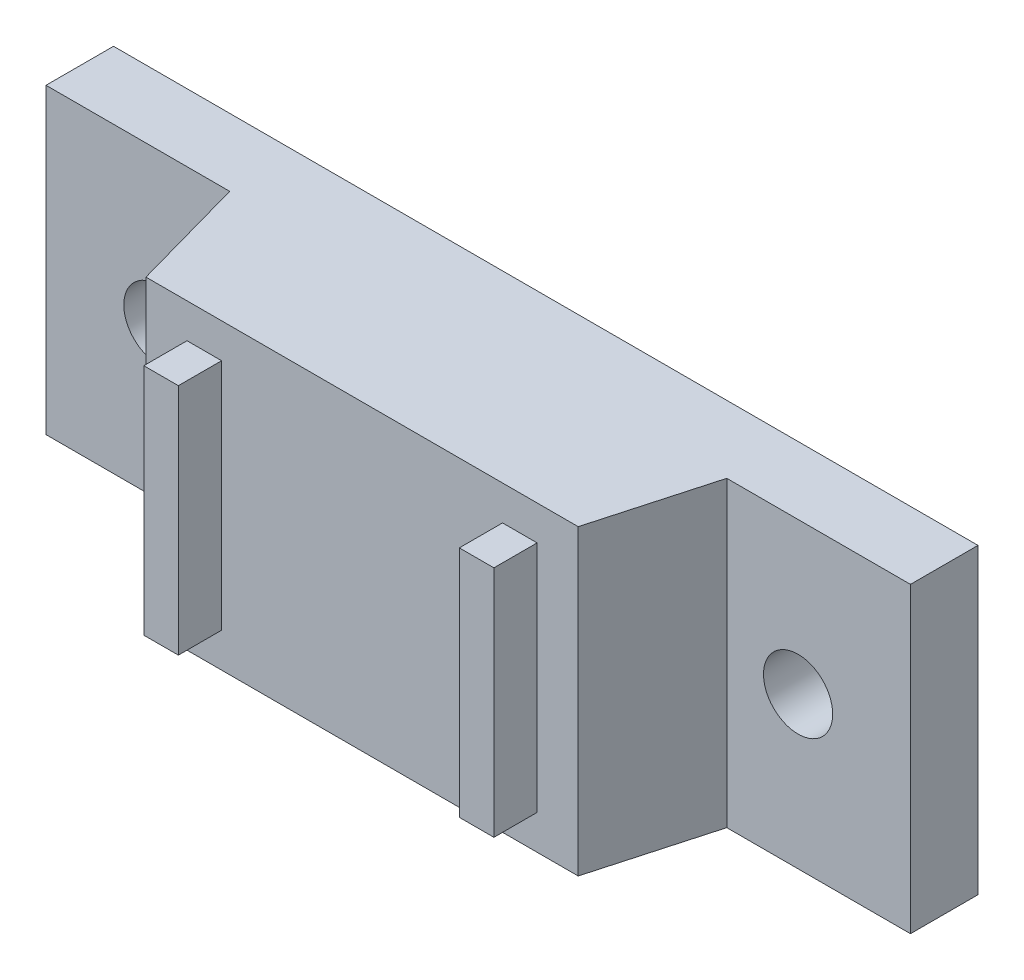
SolidWorks part; units mm, degrees
ref_plane "Front" through (0, 0, 0) normal (0, 0, 1) x (1, 0, 0)
ref_plane "Top" through (0, 0, 0) normal (0, 1, 0) x (1, 0, 0)
ref_plane "Right" through (0, 0, 0) normal (1, 0, 0) x (0, 0, -1)
sketch "Sketch1" plane through (0, 0, 0) normal (0, 0, 1) x (1, 0, 0)
  line L0 (0, 18.796) -> (0, -18.796) construction
  line L1 (8.89, -25.4) -> (-8.89, -25.4)
  line L2 (8.89, -25.4) -> (8.89, 25.4)
  line L3 (8.89, 25.4) -> (-8.89, 25.4)
  line L4 (-8.89, -25.4) -> (-8.89, 25.4)
  line L5 (8.89, -25.4) -> (-8.89, 25.4) construction
  line L6 (8.89, 25.4) -> (-8.89, -25.4) construction
  circle A0 centre (0, 18.796) radius 2.032
  circle A1 centre (0, -18.796) radius 2.032
  point P0 (0, 0)
  point P8 (0, 0)
  dimension "D3" = 4.064
  dimension "D1" = 17.78
  dimension "D2" = 50.8
  dimension "D4" = 37.592
extrude "Boss-Extrude1" add sketch "Sketch1" along normal blind 3.9688
sketch "Sketch2" plane through (0, 0, 3.9688) normal (0, 0, 1) x (1, 0, 0)
  line L0 (8.89, -25.4) -> (8.89, 25.4) construction
  line L1 (-8.89, -14.605) -> (8.89, -14.605)
  line L2 (-8.89, -14.605) -> (-8.89, 14.605)
  line L3 (-8.89, 14.605) -> (8.89, 14.605)
  line L4 (8.89, -14.605) -> (8.89, 14.605)
  line L5 (-8.89, -14.605) -> (8.89, 14.605) construction
  line L6 (-8.89, 14.605) -> (8.89, -14.605) construction
  point P0 (0, 0)
  dimension "D1" = 29.21
ref_plane "Plane1" through (0, 0, 10.795) normal (0, 0, 1) x (1, 0, 0)
sketch "Sketch3" plane through (0, 0, 10.795) normal (0, 0, 1) x (1, 0, 0)
  line L0 (-8.89, 25.4) -> (-8.89, -25.4) construction
  line L1 (8.89, -12.7) -> (-8.89, -12.7)
  line L2 (8.89, -12.7) -> (8.89, 12.7)
  line L3 (8.89, 12.7) -> (-8.89, 12.7)
  line L4 (-8.89, -12.7) -> (-8.89, 12.7)
  line L5 (8.89, -12.7) -> (-8.89, 12.7) construction
  line L6 (8.89, 12.7) -> (-8.89, -12.7) construction
  point P0 (0, 0)
  dimension "D1" = 25.4
loft "Loft1" add profiles "Sketch3", "Sketch2"
sketch "Sketch4" plane through (0, 0, 10.795) normal (0, 0, 1) x (1, 0, 0)
  line L0 (0, 0) -> (6.858, 0) construction
  line L4 (-6.858, 10.287) -> (-6.858, 8.255)
  line L5 (-6.858, 8.255) -> (6.858, 8.255)
  line L6 (6.858, 8.255) -> (6.858, 10.287)
  line L7 (6.858, -10.287) -> (6.858, -8.255)
  line L8 (-6.858, 10.668) -> (-6.858, -10.668)
  line L9 (-6.858, -10.668) -> (6.858, -10.668)
  line L10 (6.858, -10.668) -> (6.858, 10.668)
  line L11 (6.858, 10.668) -> (-6.858, 10.668)
  line L12 (-6.858, 10.287) -> (-6.858, -10.287) construction
  line L13 (-6.858, -10.287) -> (6.858, -10.287)
  line L14 (6.858, -10.287) -> (6.858, 10.287) construction
  line L15 (6.858, 10.287) -> (-6.858, 10.287)
  line L16 (6.858, -8.255) -> (-6.858, -8.255)
  line L17 (-6.858, -8.255) -> (-6.858, -10.287)
  dimension "D2" = 2.032
  dimension "D3" = 16.51
  dimension "D1" = 2.032
extrude "Boss-Extrude2" add sketch "Sketch4" along normal blind 2.54
sketch "Sketch6" plane through (0, 0, 0) normal (0, 1, 0) x (1, 0, 0)
  line L0 (0, 0) -> (0, -13.335) construction
  line L2 (9.525, -13.335) -> (-6.985, -13.335)
  line L3 (-9.525, -15.875) -> (-9.525, -31.877)
  line L4 (-9.525, -13.335) -> (9.525, -13.335) construction
  line L5 (6.858, -13.335) -> (-6.858, -13.335) construction
  arc A0 (-6.985, -13.335) -> (-9.525, -15.875) centre (-6.985, -15.875) ccw
  point P3 (0, -13.335)
  point P11 (-9.525, -13.335)
  dimension "D2" = 2.54
  dimension "D1" = 19.05
  dimension "D3" = 18.542
extrude "Extrude-Thin1" add sketch "Sketch6" along normal mid plane 28.575 separate body thin thin type one direction reverse wall 0.9525
fillet "Fillet1" radius 2.54 4 edges at (-9.0487, 14.2875, 31.877) (-9.0487, -14.2875, 31.877) (9.525, -14.2875, 13.8113) (9.525, 14.2875, 13.8113)
sketch "Sketch7" plane through (-9.525, 0, 0) normal (-1, 0, 0) x (0, 0, 1)
  line L0 (0, 0) -> (22.2885, 0) construction
  line L1 (22.2885, 0) -> (22.2885, 9.525) construction
  line L2 (22.2885, 0) -> (22.2885, -9.525) construction
  line L3 (19.304, 9.525) -> (25.273, 9.525) construction
  line L4 (19.304, 11.303) -> (25.273, 11.303)
  line L5 (19.304, 7.747) -> (25.273, 7.747)
  line L6 (19.304, -9.525) -> (25.273, -9.525) construction
  line L7 (19.304, -7.747) -> (25.273, -7.747)
  line L8 (19.304, -11.303) -> (25.273, -11.303)
  line L9 (27.051, 9.525) -> (31.877, 9.525) construction
  line L10 (31.877, 11.7475) -> (31.877, -11.7475) construction
  arc A0 (19.304, 11.303) -> (19.304, 7.747) centre (19.304, 9.525) ccw
  arc A1 (25.273, 7.747) -> (25.273, 11.303) centre (25.273, 9.525) ccw
  arc A2 (19.304, -7.747) -> (19.304, -11.303) centre (19.304, -9.525) ccw
  arc A3 (25.273, -11.303) -> (25.273, -7.747) centre (25.273, -9.525) ccw
  point P7 (22.2885, 9.525)
  point P13 (22.2885, -9.525)
  dimension "D3" = 9.525
  dimension "D1" = 3.556
  dimension "D2" = 19.05
  dimension "D4" = 4.826
extrude "Cut-Extrude1" cut sketch "Sketch7" against normal up to surface (0.9525 mm away) up to face at (-8.5725, 0, 25.8717)
sketch "Sketch8" plane through (-8.5725, 0, 0) normal (1, 0, 0) x (0, 0, -1)
  line L0 (-31.877, 0) -> (-30.353, 0) construction
  line L1 (-31.877, 11.7475) -> (-31.877, -11.7475) construction
  line L2 (-30.353, 0) -> (-29.083, 0) construction
  circle A0 centre (-29.083, 0) radius 1.27
  dimension "D1" = 2.54
  dimension "D2" = 1.524
extrude "Cut-Extrude2" cut sketch "Sketch8" against normal up to surface (0.9525 mm away) up to face at (-9.525, -9.525, 22.2885)
move or copy body "Body-Move/Copy1" bodies to move or copy 114 copy no translate (0, 0, 25.4)
delete or keep bodies "Body-Delete1" type delete bodies bodies 115
delete or keep bodies "Body-Delete2" [suppressed] type delete bodies bodies 111
move or copy body "Body-Move/Copy2" [suppressed] bodies to move or copy 111 115 copy no rotation origin (0, 0, 0) rotation axis (0, 0, 1) rotation angle 90
move or copy body "Body-Move/Copy3" bodies to move or copy 111 copy no rotation origin (0, 0, 0) rotation axis (0, 0, 1) rotation angle 90
move or copy body "Body-Move/Copy4" [suppressed] bodies to move or copy 114 copy no rotation origin (0, 0, 0) rotation axis (0, 0, 1) rotation angle 90
sketch "Sketch9" [suppressed] plane through (0, -8.5725, 0) normal (0, 1, 0) x (1, 0, 0)
  line L0 (-4.7625, -25.527) -> (-4.7625, -31.877)
  line L1 (-11.7475, -31.877) -> (11.7475, -31.877) construction
  line L2 (4.7625, -25.527) -> (4.7625, -31.877)
  line L3 (4.7625, -31.877) -> (-4.7625, -31.877)
  arc A0 (4.7625, -25.527) -> (-4.7625, -25.527) centre (0, -25.527) ccw
  dimension "D1" = 9.525
  dimension "D2" = 6.35
extrude "Cut-Extrude3" [suppressed] cut sketch "Sketch9" against normal through all
